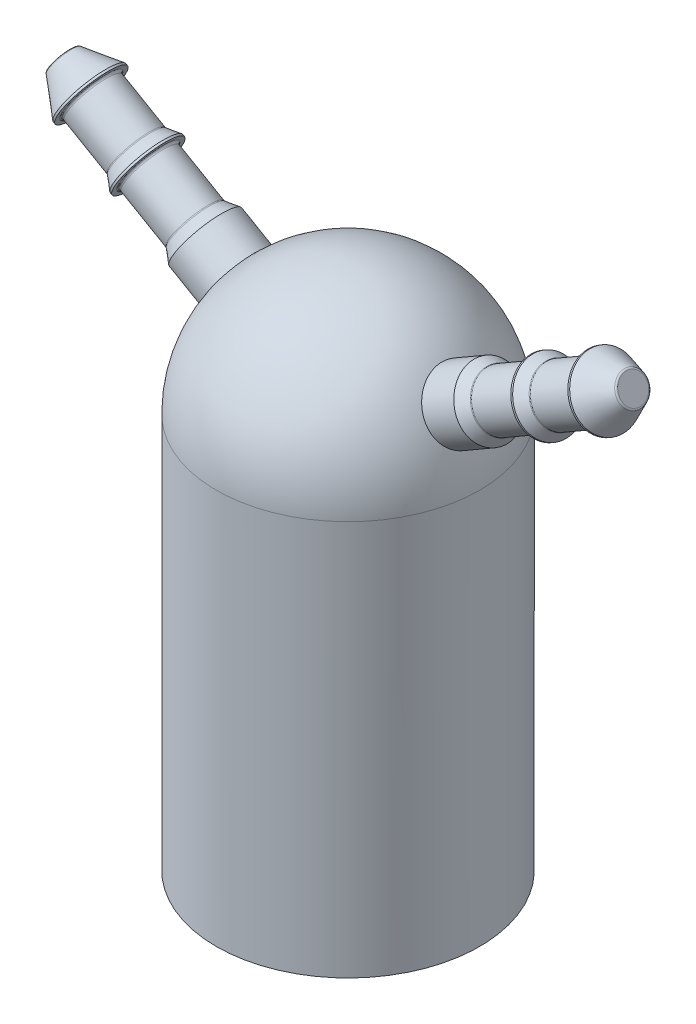
SolidWorks part; units mm, degrees
ref_plane "Front Plane" through (0, 0, 0) normal (0, 0, 1) x (1, 0, 0)
ref_plane "Top Plane" through (0, 0, 0) normal (0, 1, 0) x (1, 0, 0)
ref_plane "Right Plane" through (0, 0, 0) normal (1, 0, 0) x (0, 0, -1)
sketch "Sketch1" plane through (0, 0, 0) normal (0, 0, 1) x (1, 0, 0)
  line L0 (0, 0) -> (0, 25.4)
  line L1 (-6.35, 19.05) -> (-6.35, 0)
  line L2 (-6.35, 0) -> (0, 0)
  arc A0 (0, 25.4) -> (-6.35, 19.05) centre (0, 19.05) ccw
  dimension "D1" = 6.35
  dimension "D2" = 25.4
revolve "Revolve1" add sketch "Sketch1" angle 360 about L0
sketch "Sketch2" plane through (0, 0, 0) normal (0, -1, 0) x (1, 0, 0)
  line L0 (2.8759, 3.0527) -> (2.4916, 2.6447)
  line L1 (3.1467, 1.8168) -> (3.6321, 2.097)
  line L2 (4.0169, 1.2057) -> (3.4801, 1.0446)
  line L3 (3.6335, 0) -> (4.194, 0)
  line L4 (4.0816, -0.9643) -> (3.5362, -0.8354)
  line L5 (3.1467, -1.8168) -> (3.6321, -2.097)
  line L6 (3.0527, -2.8759) -> (2.6447, -2.4916)
  line L7 (1.8168, -3.1467) -> (2.097, -3.6321)
  line L8 (1.2057, -4.0169) -> (1.0446, -3.4801)
  line L9 (0, -3.6335) -> (0, -4.194)
  line L10 (-0.9643, -4.0816) -> (-0.8354, -3.5362)
  line L11 (-1.8168, -3.1467) -> (-2.097, -3.6321)
  line L12 (-2.8759, -3.0527) -> (-2.4916, -2.6447)
  line L13 (-3.1467, -1.8168) -> (-3.6321, -2.097)
  line L14 (-4.0169, -1.2057) -> (-3.4801, -1.0446)
  line L15 (-3.6335, 0) -> (-4.194, 0)
  line L16 (-4.0816, 0.9643) -> (-3.5362, 0.8354)
  line L17 (-3.1467, 1.8168) -> (-3.6321, 2.097)
  line L18 (-3.0527, 2.8759) -> (-2.6447, 2.4916)
  line L19 (-1.8168, 3.1467) -> (-2.097, 3.6321)
  line L20 (-1.2057, 4.0169) -> (-1.0446, 3.4801)
  line L21 (0, 3.6335) -> (0, 4.194)
  line L22 (0.9643, 4.0816) -> (0.8354, 3.5362)
  line L23 (1.8168, 3.1467) -> (2.097, 3.6321)
  arc A0 (1.8168, 3.1467) -> (1.8515, 3.0094) centre (1.9047, 3.0959) ccw
  arc A1 (2.35, 2.6385) -> (1.8515, 3.0094) centre (0, 0) ccw
  arc A2 (2.35, 2.6385) -> (2.4916, 2.6447) centre (2.4176, 2.7144) ccw
  arc A3 (4.2225, 3.0468) -> (3.936, 3.4089) centre (0, 0) ccw
  arc A4 (3.1467, 1.8168) -> (3.1081, 1.6804) centre (3.1975, 1.7288) ccw
  arc A5 (3.3544, 1.11) -> (3.1081, 1.6804) centre (0, 0) ccw
  arc A6 (3.3544, 1.11) -> (3.4801, 1.0446) centre (3.4509, 1.1419) ccw
  arc A7 (5.1802, 0.5273) -> (5.1131, 0.9842) centre (0, 0) ccw
  arc A8 (3.6335, 0) -> (3.5319, -0.0988) centre (3.6335, -0.1016) ccw
  arc A9 (3.46, -0.7159) -> (3.5319, -0.0988) centre (0, 0) ccw
  arc A10 (3.46, -0.7159) -> (3.5362, -0.8354) centre (3.5595, -0.7365) ccw
  arc A11 (4.7499, -2.1334) -> (4.9202, -1.7042) centre (0, 0) ccw
  arc A12 (3.1467, -1.8168) -> (3.0094, -1.8515) centre (3.0959, -1.9047) ccw
  arc A13 (2.6385, -2.35) -> (3.0094, -1.8515) centre (0, 0) ccw
  arc A14 (2.6385, -2.35) -> (2.6447, -2.4916) centre (2.7144, -2.4176) ccw
  arc A15 (3.0468, -4.2225) -> (3.4089, -3.936) centre (0, 0) ccw
  arc A16 (1.8168, -3.1467) -> (1.6804, -3.1081) centre (1.7288, -3.1975) ccw
  arc A17 (1.11, -3.3544) -> (1.6804, -3.1081) centre (0, 0) ccw
  arc A18 (1.11, -3.3544) -> (1.0446, -3.4801) centre (1.1419, -3.4509) ccw
  arc A19 (0.5273, -5.1802) -> (0.9842, -5.1131) centre (0, 0) ccw
  arc A20 (0, -3.6335) -> (-0.0988, -3.5319) centre (-0.1016, -3.6335) ccw
  arc A21 (-0.7159, -3.46) -> (-0.0988, -3.5319) centre (0, 0) ccw
  arc A22 (-0.7159, -3.46) -> (-0.8354, -3.5362) centre (-0.7365, -3.5595) ccw
  arc A23 (-2.1334, -4.7499) -> (-1.7042, -4.9202) centre (0, 0) ccw
  arc A24 (-1.8168, -3.1467) -> (-1.8515, -3.0094) centre (-1.9047, -3.0959) ccw
  arc A25 (-2.35, -2.6385) -> (-1.8515, -3.0094) centre (0, 0) ccw
  arc A26 (-2.35, -2.6385) -> (-2.4916, -2.6447) centre (-2.4176, -2.7144) ccw
  arc A27 (-4.2225, -3.0468) -> (-3.936, -3.4089) centre (0, 0) ccw
  arc A28 (-3.1467, -1.8168) -> (-3.1081, -1.6804) centre (-3.1975, -1.7288) ccw
  arc A29 (-3.3544, -1.11) -> (-3.1081, -1.6804) centre (0, 0) ccw
  arc A30 (-3.3544, -1.11) -> (-3.4801, -1.0446) centre (-3.4509, -1.1419) ccw
  arc A31 (-5.1802, -0.5273) -> (-5.1131, -0.9842) centre (0, 0) ccw
  arc A32 (-3.6335, 0) -> (-3.5319, 0.0988) centre (-3.6335, 0.1016) ccw
  arc A33 (-3.46, 0.7159) -> (-3.5319, 0.0988) centre (0, 0) ccw
  arc A34 (-3.46, 0.7159) -> (-3.5362, 0.8354) centre (-3.5595, 0.7365) ccw
  arc A35 (-4.7499, 2.1334) -> (-4.9202, 1.7042) centre (0, 0) ccw
  arc A36 (-3.1467, 1.8168) -> (-3.0094, 1.8515) centre (-3.0959, 1.9047) ccw
  arc A37 (-2.6385, 2.35) -> (-3.0094, 1.8515) centre (0, 0) ccw
  arc A38 (-2.6385, 2.35) -> (-2.6447, 2.4916) centre (-2.7144, 2.4176) ccw
  arc A39 (-3.0468, 4.2225) -> (-3.4089, 3.936) centre (0, 0) ccw
  arc A40 (-1.8168, 3.1467) -> (-1.6804, 3.1081) centre (-1.7288, 3.1975) ccw
  arc A41 (-1.11, 3.3544) -> (-1.6804, 3.1081) centre (0, 0) ccw
  arc A42 (-1.11, 3.3544) -> (-1.0446, 3.4801) centre (-1.1419, 3.4509) ccw
  arc A43 (-0.5273, 5.1802) -> (-0.9842, 5.1131) centre (0, 0) ccw
  arc A44 (0, 3.6335) -> (0.0988, 3.5319) centre (0.1016, 3.6335) ccw
  arc A45 (0.7159, 3.46) -> (0.0988, 3.5319) centre (0, 0) ccw
  arc A46 (0.7159, 3.46) -> (0.8354, 3.5362) centre (0.7365, 3.5595) ccw
  arc A47 (2.1334, 4.7499) -> (1.7042, 4.9202) centre (0, 0) ccw
  spline S0 degree 3 poles (2.8759, 3.0527) (2.9091, 3.0864) (2.9492, 3.1125) (3.0296, 3.1624) (3.1549, 3.2295) (3.2882, 3.2794) (3.5598, 3.3619) (3.7472, 3.3939) (3.936, 3.4089) knots 0 0 0 0 0.125 0.125 0.25 0.5 0.5 1 1 1 1
  spline S1 degree 3 poles (4.0169, 1.2057) (4.0625, 1.2184) (4.1103, 1.221) (4.2049, 1.2239) (4.347, 1.2194) (4.4874, 1.196) (4.7638, 1.1316) (4.9422, 1.0656) (5.1131, 0.9842) knots 0 0 0 0 0.125 0.125 0.25 0.5 0.5 1 1 1 1
  spline S2 degree 3 poles (4.0816, -0.9643) (4.1274, -0.9761) (4.1701, -0.9978) (4.2535, -1.0425) (4.3743, -1.1174) (4.4842, -1.208) (4.6914, -1.4019) (4.8129, -1.5482) (4.9202, -1.7042) knots 0 0 0 0 0.125 0.125 0.25 0.5 0.5 1 1 1 1
  spline S3 degree 3 poles (3.0527, -2.8759) (3.0864, -2.9091) (3.1125, -2.9492) (3.1624, -3.0296) (3.2295, -3.1549) (3.2794, -3.2882) (3.3619, -3.5598) (3.3939, -3.7472) (3.4089, -3.936) knots 0 0 0 0 0.125 0.125 0.25 0.5 0.5 1 1 1 1
  spline S4 degree 3 poles (1.2057, -4.0169) (1.2184, -4.0625) (1.221, -4.1103) (1.2239, -4.2049) (1.2194, -4.347) (1.196, -4.4874) (1.1316, -4.7638) (1.0656, -4.9422) (0.9842, -5.1131) knots 0 0 0 0 0.125 0.125 0.25 0.5 0.5 1 1 1 1
  spline S5 degree 3 poles (-0.9643, -4.0816) (-0.9761, -4.1274) (-0.9978, -4.1701) (-1.0425, -4.2535) (-1.1174, -4.3743) (-1.208, -4.4842) (-1.4019, -4.6914) (-1.5482, -4.8129) (-1.7042, -4.9202) knots 0 0 0 0 0.125 0.125 0.25 0.5 0.5 1 1 1 1
  spline S6 degree 3 poles (-2.8759, -3.0527) (-2.9091, -3.0864) (-2.9492, -3.1125) (-3.0296, -3.1624) (-3.1549, -3.2295) (-3.2882, -3.2794) (-3.5598, -3.3619) (-3.7472, -3.3939) (-3.936, -3.4089) knots 0 0 0 0 0.125 0.125 0.25 0.5 0.5 1 1 1 1
  spline S7 degree 3 poles (-4.0169, -1.2057) (-4.0625, -1.2184) (-4.1103, -1.221) (-4.2049, -1.2239) (-4.347, -1.2194) (-4.4874, -1.196) (-4.7638, -1.1316) (-4.9422, -1.0656) (-5.1131, -0.9842) knots 0 0 0 0 0.125 0.125 0.25 0.5 0.5 1 1 1 1
  spline S8 degree 3 poles (-4.0816, 0.9643) (-4.1274, 0.9761) (-4.1701, 0.9978) (-4.2535, 1.0425) (-4.3743, 1.1174) (-4.4842, 1.208) (-4.6914, 1.4019) (-4.8129, 1.5482) (-4.9202, 1.7042) knots 0 0 0 0 0.125 0.125 0.25 0.5 0.5 1 1 1 1
  spline S9 degree 3 poles (-3.0527, 2.8759) (-3.0864, 2.9091) (-3.1125, 2.9492) (-3.1624, 3.0296) (-3.2295, 3.1549) (-3.2794, 3.2882) (-3.3619, 3.5598) (-3.3939, 3.7472) (-3.4089, 3.936) knots 0 0 0 0 0.125 0.125 0.25 0.5 0.5 1 1 1 1
  spline S10 degree 3 poles (-1.2057, 4.0169) (-1.2184, 4.0625) (-1.221, 4.1103) (-1.2239, 4.2049) (-1.2194, 4.347) (-1.196, 4.4874) (-1.1316, 4.7638) (-1.0656, 4.9422) (-0.9842, 5.1131) knots 0 0 0 0 0.125 0.125 0.25 0.5 0.5 1 1 1 1
  spline S11 degree 3 poles (-0.5273, 5.1802) (-0.4002, 5.0399) (-0.2857, 4.888) (-0.1446, 4.6418) (-0.1027, 4.5566) (-0.0517, 4.4242) (-0.0366, 4.3792) (-0.0123, 4.2878) (-0.001, 4.2413) (0, 4.194) knots 0 0 0 0 0.5 0.5 0.75 0.75 0.875 0.875 1 1 1 1
  spline S12 degree 3 poles (0.9643, 4.0816) (0.9761, 4.1274) (0.9978, 4.1701) (1.0425, 4.2535) (1.1174, 4.3743) (1.208, 4.4842) (1.4019, 4.6914) (1.5482, 4.8129) (1.7042, 4.9202) knots 0 0 0 0 0.125 0.125 0.25 0.5 0.5 1 1 1 1
  spline S13 degree 3 poles (-4.7499, 2.1334) (-4.5648, 2.1734) (-4.376, 2.1966) (-4.0922, 2.1956) (-3.9975, 2.1893) (-3.8573, 2.1673) (-3.8108, 2.1579) (-3.7195, 2.1333) (-3.6736, 2.1198) (-3.6321, 2.097) knots 0 0 0 0 0.5 0.5 0.75 0.75 0.875 0.875 1 1 1 1
  spline S14 degree 3 poles (4.2225, 3.0468) (4.1646, 2.8665) (4.0903, 2.6915) (3.9476, 2.4461) (3.8948, 2.3673) (3.8056, 2.2568) (3.7742, 2.2213) (3.7072, 2.1545) (3.6726, 2.1215) (3.6321, 2.097) knots 0 0 0 0 0.5 0.5 0.75 0.75 0.875 0.875 1 1 1 1
  spline S15 degree 3 poles (4.7499, -2.1334) (4.5648, -2.1734) (4.376, -2.1966) (4.0922, -2.1956) (3.9975, -2.1893) (3.8573, -2.1673) (3.8108, -2.1579) (3.7195, -2.1333) (3.6736, -2.1198) (3.6321, -2.097) knots 0 0 0 0 0.5 0.5 0.75 0.75 0.875 0.875 1 1 1 1
  spline S16 degree 3 poles (2.1334, 4.7499) (2.1734, 4.5648) (2.1966, 4.376) (2.1956, 4.0922) (2.1893, 3.9975) (2.1673, 3.8573) (2.1579, 3.8108) (2.1333, 3.7195) (2.1198, 3.6736) (2.097, 3.6321) knots 0 0 0 0 0.5 0.5 0.75 0.75 0.875 0.875 1 1 1 1
  spline S17 degree 3 poles (0.5273, -5.1802) (0.4002, -5.0399) (0.2857, -4.888) (0.1446, -4.6418) (0.1027, -4.5566) (0.0517, -4.4242) (0.0366, -4.3792) (0.0123, -4.2878) (0.001, -4.2413) (0, -4.194) knots 0 0 0 0 0.5 0.5 0.75 0.75 0.875 0.875 1 1 1 1
  spline S18 degree 3 poles (-5.1802, -0.5273) (-5.0399, -0.4002) (-4.888, -0.2857) (-4.6418, -0.1446) (-4.5566, -0.1027) (-4.4242, -0.0517) (-4.3792, -0.0366) (-4.2878, -0.0123) (-4.2413, -0.001) (-4.194, 0) knots 0 0 0 0 0.5 0.5 0.75 0.75 0.875 0.875 1 1 1 1
  spline S19 degree 3 poles (3.0468, -4.2225) (2.8665, -4.1646) (2.6915, -4.0903) (2.4461, -3.9476) (2.3673, -3.8948) (2.2568, -3.8056) (2.2213, -3.7742) (2.1545, -3.7072) (2.1215, -3.6726) (2.097, -3.6321) knots 0 0 0 0 0.5 0.5 0.75 0.75 0.875 0.875 1 1 1 1
  spline S20 degree 3 poles (-3.0468, 4.2225) (-2.8665, 4.1646) (-2.6915, 4.0903) (-2.4461, 3.9476) (-2.3673, 3.8948) (-2.2568, 3.8056) (-2.2213, 3.7742) (-2.1545, 3.7072) (-2.1215, 3.6726) (-2.097, 3.6321) knots 0 0 0 0 0.5 0.5 0.75 0.75 0.875 0.875 1 1 1 1
  spline S21 degree 3 poles (5.1802, 0.5273) (5.0399, 0.4002) (4.888, 0.2857) (4.6418, 0.1446) (4.5566, 0.1027) (4.4242, 0.0517) (4.3792, 0.0366) (4.2878, 0.0123) (4.2413, 0.001) (4.194, 0) knots 0 0 0 0 0.5 0.5 0.75 0.75 0.875 0.875 1 1 1 1
  spline S22 degree 3 poles (-2.1334, -4.7499) (-2.1734, -4.5648) (-2.1966, -4.376) (-2.1956, -4.0922) (-2.1893, -3.9975) (-2.1673, -3.8573) (-2.1579, -3.8108) (-2.1333, -3.7195) (-2.1198, -3.6736) (-2.097, -3.6321) knots 0 0 0 0 0.5 0.5 0.75 0.75 0.875 0.875 1 1 1 1
  spline S23 degree 3 poles (-4.2225, -3.0468) (-4.1646, -2.8665) (-4.0903, -2.6915) (-3.9476, -2.4461) (-3.8948, -2.3673) (-3.8056, -2.2568) (-3.7742, -2.2213) (-3.7072, -2.1545) (-3.6726, -2.1215) (-3.6321, -2.097) knots 0 0 0 0 0.5 0.5 0.75 0.75 0.875 0.875 1 1 1 1
extrude "Cut-Extrude1" cut sketch "Sketch2" against normal blind 12.7
sketch "Sketch3" plane through (0, 0, 0) normal (0, 0, 1) x (1, 0, 0)
  line L0 (0, 19.05) -> (-13.7482, 26.9875) construction
  line L1 (6.35, 19.05) -> (-6.35, 19.05) construction
  line L2 (-13.7482, 26.9875) -> (-14.113, 26.3556)
  line L3 (-14.113, 26.3556) -> (-13.2551, 24.8697)
  line L4 (-13.2551, 24.8697) -> (-13.1671, 24.8189)
  line L5 (-13.1671, 24.8189) -> (-13.0083, 25.0939)
  line L6 (-13.0083, 25.0939) -> (-10.8229, 23.8322)
  line L7 (-10.8229, 23.8322) -> (-10.5054, 23.2822)
  line L8 (-10.5054, 23.2822) -> (-10.4175, 23.2314)
  line L9 (-10.4175, 23.2314) -> (-10.2587, 23.5064)
  line L10 (-10.2587, 23.5064) -> (-7.9853, 22.1939)
  line L11 (-7.9853, 22.1939) -> (-7.6678, 21.6439)
  line L12 (0, 19.05) -> (-13.7482, 26.9875)
  line L14 (0, 19.05) -> (-0.7937, 17.6752)
  line L15 (-0.7937, 17.6752) -> (-7.6678, 21.6439)
  point P4 (-6.807, 23.5795)
  point P14 (-9.3153, 26.5692)
  dimension "D1" = 3.175
  dimension "D2" = 2.54
  dimension "D3" = 0.1016
  dimension "D4" = 1.5875
  dimension "D5" = 30
  dimension "D6" = 4.7625
  dimension "D7" = 7.9375
  dimension "D8" = 30
  dimension "D9" = 15.875
revolve "Revolve2" add sketch "Sketch3" angle 360 about L0
fillet "Fillet1" radius 0.1016 5 edges at (-8.9887, 25.7061, 0) (-11.7383, 27.2936, 0) (-13.3833, 27.6194, 0) (-9.5529, 26.0319, 0) (-6.7153, 24.3936, 0)
mirror "Mirror1" about plane through (0, 0, 0) normal (1, 0, 0) of "Fillet1", "Revolve2"
